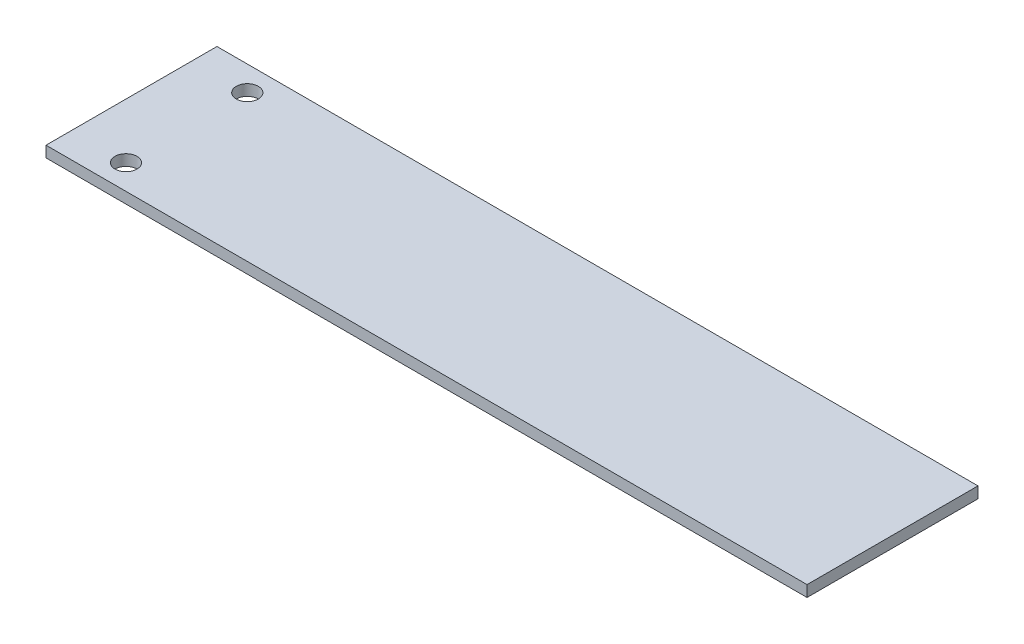
SolidWorks part; units mm, degrees
ref_plane "Front Plane" through (0, 0, 0) normal (0, 0, 1) x (1, 0, 0)
ref_plane "Top Plane" through (0, 0, 0) normal (0, 1, 0) x (1, 0, 0)
ref_plane "Right Plane" through (0, 0, 0) normal (1, 0, 0) x (0, 0, -1)
sketch "Sketch1" plane through (0, 0, 0) normal (0, 1, 0) x (1, 0, 0)
  line L0 (-11.8013, -7.9901) -> (7.1987, -7.9901)
  line L1 (-11.8013, -7.9901) -> (-11.8013, 7.5099)
  line L2 (7.1987, -7.9901) -> (7.1987, 7.5099)
  line L3 (-11.8013, 7.5099) -> (7.1987, 7.5099)
  dimension "D1" = 19
  dimension "D2" = 15.5
extrude "Boss-Extrude1" add sketch "Sketch1" along normal blind 1
hole_wizard "Ø1.0mm Dowel Hole1" positions "Sketch2" profile "Sketch3" hole size "Ø1.0" standard "ANSI Metric"
sketch "Sketch2" plane through (0, 1, 0) normal (0, 1, 0) x (1, 0, 0)
  line L0 (-11.8013, 7.5099) -> (-11.8013, -7.9901) construction
  line L1 (-11.8013, -7.9901) -> (7.1987, -7.9901) construction
  point P0 (-6.8013, 5.2599)
  point P2 (-6.8013, -5.7401)
  dimension "D1" = 11
  dimension "D2" = 5
  dimension "D3" = 2.25
sketch "Sketch3" plane through (-6.8013, 1, -5.2599) normal (1, 0, 0) x (0, 0, 1)
  line L0 (0, 0) -> (0, 25.6009)
  line L1 (0, 25.6009) -> (1, 25)
  line L2 (1, 25) -> (1, 0)
  line L5 (1, 0) -> (0, 0)
  line L10 (0, 25.6009) -> (-1, 25) construction
  line L11 (0, -6.35) -> (0, 107.95) construction
  dimension "Hole Dia." = 2
  dimension "Hole Depth" = 25
  dimension "Drill Angle" = 118
sketch "Sketch4" plane through (7.1987, 0, 0) normal (1, 0, 0) x (0, 0, -1)
  line L0 (-7.9901, 1) -> (7.5099, 1)
  line L1 (-7.9901, 1) -> (-7.9901, -0.0159)
  line L2 (7.5099, 1) -> (7.5099, -0.0159)
  line L3 (-7.9901, -0.0159) -> (7.5099, -0.0159)
extrude "Boss-Extrude2" add sketch "Sketch4" along normal blind 50
